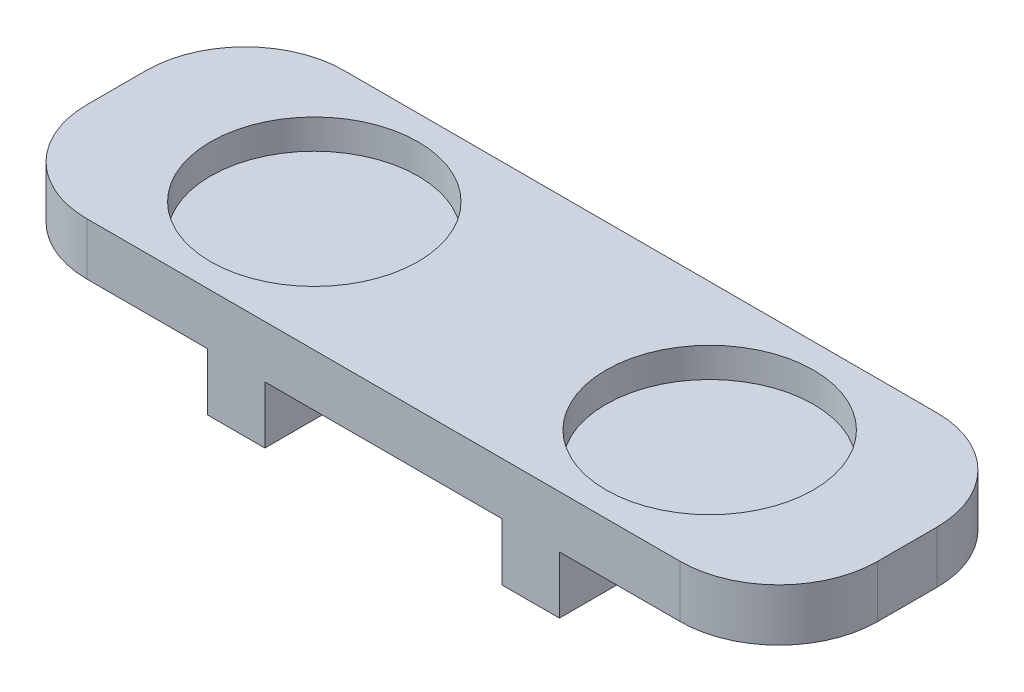
SolidWorks part; units mm, degrees
material "3D printer PLA"
ref_plane "Front Plane" through (0, 0, 0) normal (0, 0, 1) x (1, 0, 0)
ref_plane "Top Plane" through (0, 0, 0) normal (0, 1, 0) x (1, 0, 0)
ref_plane "Right Plane" through (0, 0, 0) normal (1, 0, 0) x (0, 0, -1)
sketch "Sketch1" plane through (0, 0, 0) normal (0, 0, 1) x (1, 0, 0)
  line L0 (0, 0) -> (128.0045, 0) construction
  line L1 (64.0023, 0) -> (64.0023, 28.6255) construction
  line L2 (48.7623, -7.366) -> (41.3963, 0) construction
  line L3 (79.2423, 0) -> (86.6083, 0)
  line L4 (79.2423, 0) -> (79.2423, -7.366)
  line L5 (79.2423, -7.366) -> (86.6083, -7.366)
  line L6 (86.6083, 0) -> (86.6083, -7.366)
  line L7 (79.2423, 0) -> (86.6083, -7.366) construction
  line L8 (79.2423, -7.366) -> (86.6083, 0) construction
  line L9 (48.7623, 0) -> (41.3963, -7.366) construction
  line L10 (41.3963, 0) -> (41.3963, -7.366)
  line L11 (48.7623, -7.366) -> (41.3963, -7.366)
  line L12 (48.7623, 0) -> (48.7623, -7.366)
  line L13 (48.7623, 0) -> (41.3963, 0)
  line L14 (41.3963, 0) -> (13.2023, 0)
  line L15 (13.2023, 0) -> (13.2023, 6.7093)
  line L16 (13.2023, 6.7093) -> (114.8023, 6.7093)
  line L17 (114.8023, 6.7093) -> (114.8023, 0)
  line L18 (114.8023, 0) -> (86.6083, 0)
  line L19 (48.7623, 0) -> (79.2423, 0)
  point P9 (82.9253, -3.683)
  point P14 (45.0793, -3.683)
  point P15 (64.0023, 6.7093)
  point P20 (0, 0)
  dimension "D1" = 7.366
  dimension "D2" = 7.366
  dimension "D3" = 15.24
  dimension "D4" = 101.6
extrude "Boss-Extrude1" add sketch "Sketch1" along normal blind 33.02 contours L13 L19 L3 L18 L17 L16 L15 L14 | L12 L13 L10 L11 | L6 L3 L4 L5
sketch "Sketch2" plane through (0, 6.7093, 0) normal (0, 1, 0) x (1, 0, 0)
  line L0 (13.2023, -16.51) -> (114.8023, -16.51) construction
  line L1 (13.2023, -33.02) -> (13.2023, 0) construction
  line L2 (114.8023, -33.02) -> (114.8023, 0) construction
  circle A0 centre (38.6023, -16.51) radius 13.335
  circle A1 centre (89.4023, -16.51) radius 13.335
  dimension "D1" = 26.67
  dimension "D2" = 26.67
  dimension "D3" = 50.8
  dimension "D4" = 25.4
extrude "Cut-Extrude1" cut sketch "Sketch2" against normal blind 3.81
fillet "Fillet1" radius 12.7 4 edges at (114.8023, 3.3546, 0) (114.8023, 3.3546, 33.02) (13.2023, 3.3546, 0) (13.2023, 3.3546, 33.02)
